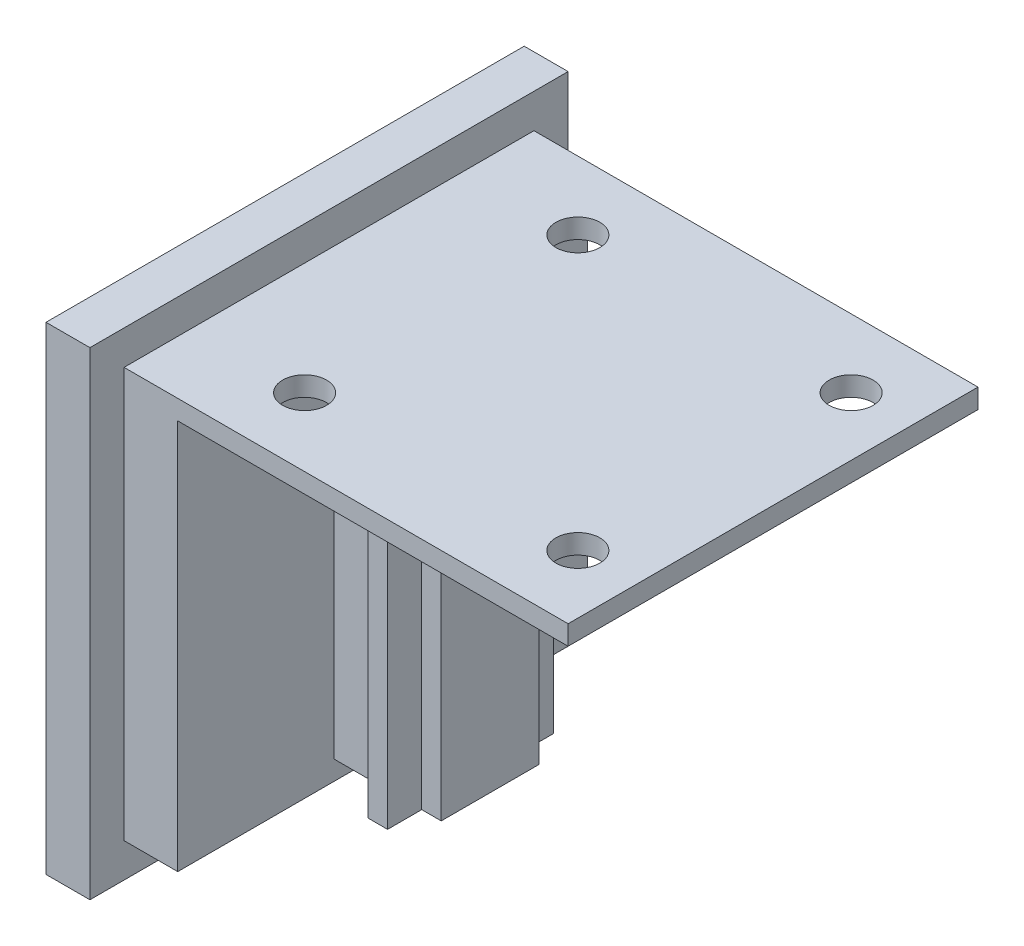
SolidWorks part; units mm, degrees
ref_plane "Front Plane" through (0, 0, 0) normal (0, 0, 1) x (1, 0, 0)
ref_plane "Top Plane" through (0, 0, 0) normal (0, 1, 0) x (1, 0, 0)
ref_plane "Right Plane" through (0, 0, 0) normal (1, 0, 0) x (0, 0, -1)
sketch "Sketch1" plane through (0, 0, 0) normal (1, 0, 0) x (0, 0, -1)
  line L1 (24.5, 24.5) -> (-24.5, 24.5)
  line L2 (24.5, 24.5) -> (24.5, -24.5)
  line L3 (24.5, -24.5) -> (-24.5, -24.5)
  line L4 (-24.5, 24.5) -> (-24.5, -24.5)
  line L5 (24.5, 24.5) -> (-24.5, -24.5) construction
  line L6 (24.5, -24.5) -> (-24.5, 24.5) construction
  point P0 (0, 0)
  dimension "D1" = 49
  dimension "D2" = 49
extrude "Boss-Extrude1" add sketch "Sketch1" along normal blind 4.5
sketch "Sketch3" plane through (4.5, 0, 0) normal (1, 0, 0) x (0, 0, -1)
  line L0 (24.5, 24.5) -> (-24.5, 24.5) construction
  line L1 (-21, 21) -> (21, 21)
  line L2 (-21, 21) -> (-21, -21)
  line L3 (-21, -21) -> (21, -21)
  line L4 (21, 21) -> (21, -21)
  line L5 (-21, 21) -> (21, -21) construction
  line L6 (-21, -21) -> (21, 21) construction
  line L7 (-24.5, 24.5) -> (-24.5, -24.5) construction
  point P0 (0, 0)
  dimension "D1" = 3.5
  dimension "D2" = 3.5
extrude "Boss-Extrude3" add sketch "Sketch3" along normal blind 5.5
sketch "Sketch4" plane through (10, 0, 0) normal (1, 0, 0) x (0, 0, -1)
  line L0 (-21, 21) -> (-21, -21) construction
  line L1 (21, 21) -> (-21, 21)
  line L2 (21, 21) -> (21, 19)
  line L3 (21, 19) -> (-21, 19)
  line L4 (-21, 21) -> (-21, 19)
  line L5 (0, 19) -> (0, 21) construction
  line L6 (21, 20) -> (-21, 20) construction
  line L7 (21, 21) -> (-21, 21) construction
  point P0 (0, 20)
  dimension "D1" = 2
  dimension "D2" = 42
  dimension "D3" = 0
extrude "Boss-Extrude4" add sketch "Sketch4" along normal blind 40
sketch "Sketch5" plane through (10, 0, 0) normal (1, 0, 0) x (0, 0, -1)
  line L1 (-5, 19) -> (5, 19)
  line L2 (-5, 19) -> (-5, -19)
  line L3 (-5, -19) -> (5, -19)
  line L4 (5, 19) -> (5, -19)
  line L5 (0, -19) -> (0, 19) construction
  line L6 (-5, 0) -> (5, 0) construction
  point P0 (0, 0)
  dimension "D1" = 38
  dimension "D2" = 10
extrude "Boss-Extrude5" add sketch "Sketch5" along normal blind 11
sketch "Sketch6" plane through (0, 0, 5) normal (0, 0, 1) x (1, 0, 0)
  line L0 (21, -19) -> (10, -19) construction
  line L1 (17, 19) -> (19, 19)
  line L2 (17, 19) -> (17, -19)
  line L3 (17, -19) -> (19, -19)
  line L4 (19, 19) -> (19, -19)
  line L5 (18, -19) -> (18, 19) construction
  line L6 (17, 0) -> (19, 0) construction
  line L7 (10, 19) -> (10, -19) construction
  point P0 (18, 0)
  dimension "D1" = 2
  dimension "D2" = 7
extrude "Boss-Extrude6" add sketch "Sketch6" along normal blind 3.5
sketch "Sketch7" plane through (0, 0, -5) normal (0, 0, -1) x (-1, 0, 0)
  line L0 (-21, -19) -> (-10, -19) construction
  line L1 (-19, 19) -> (-17, 19)
  line L2 (-19, 19) -> (-19, -19)
  line L3 (-19, -19) -> (-17, -19)
  line L4 (-17, 19) -> (-17, -19)
  line L5 (-18, -19) -> (-18, 19) construction
  line L6 (-19, 0) -> (-17, 0) construction
  line L7 (-10, -19) -> (-10, 19) construction
  point P0 (-18, 0)
  dimension "D1" = 7
  dimension "D2" = 2
extrude "Boss-Extrude7" add sketch "Sketch7" along normal blind 3.5
hole_wizard "Ø4.5 (4.5) Diameter Slot1" positions "Sketch10" profile "Sketch11" size "Ø4.5" standard "ANSI Metric" slot yes end condition through all
sketch "Sketch10" plane through (0, 19, 0) normal (0, -1, 0) x (-1, 0, 0)
  line L0 (-50, -21) -> (-50, 21) construction
  line L1 (-50, -21) -> (-10, -21) construction
  line L2 (-50, 21) -> (-10, 21) construction
  line L3 (-10, 5) -> (-10, 21) construction
  line L5 (-10, -21) -> (-10, -5) construction
  point P0 (-44, 14)
  point P2 (-44, -14)
  point P4 (-16, -14)
  point P6 (-16, 14)
  point P21 (-10, -14.8481)
  point P26 (0, 0)
  dimension "D1" = 6
  dimension "D2" = 7
  dimension "D3" = 7
  dimension "D4" = 6
  dimension "D5" = 7
  dimension "D6" = 6
  dimension "D7" = 7
  dimension "D8" = 6
sketch "Sketch11" plane through (44, 19, -14) normal (1, 0, 0) x (0, 0, -1)
  line L0 (0, 0) -> (0, 5.5)
  line L1 (0, 5.5) -> (2.25, 5.5)
  line L2 (2.25, 5.5) -> (2.25, 0)
  line L5 (2.25, 0) -> (0, 0)
  line L11 (0, -6.35) -> (0, 107.95) construction
  dimension "Thru Hole Dia." = 4.5
  dimension "Thru Hole Depth" = 5.5
